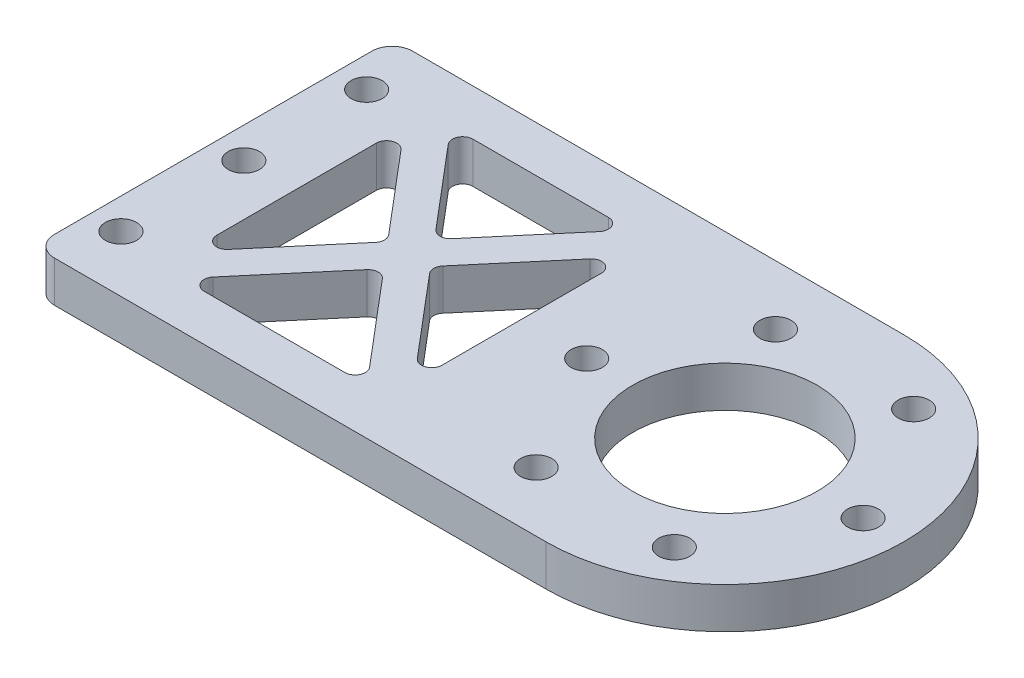
SolidWorks part; units mm, degrees
material "Thornel Mat VMA"
ref_plane "前视基准面" through (0, 0, 0) normal (0, 0, 1) x (1, 0, 0)
ref_plane "上视基准面" through (0, 0, 0) normal (0, 1, 0) x (1, 0, 0)
ref_plane "右视基准面" through (0, 0, 0) normal (1, 0, 0) x (0, 0, -1)
other "Configuration Table"
sketch "草图1" plane through (0, 0, 0) normal (0, 1, 0) x (1, 0, 0)
  line L1 (-25, -17.5) -> (25, -17.5)
  line L2 (-25, -17.5) -> (-25, 17.5)
  line L3 (-25, 17.5) -> (25, 17.5)
  line L4 (25, -17.5) -> (25, 17.5)
  line L5 (-25, -17.5) -> (25, 17.5) construction
  line L6 (-25, 17.5) -> (25, -17.5) construction
  circle A1 centre (25, 0) radius 17.5
  point P0 (0, 0)
  dimension "D1" = 35
  dimension "D2" = 35
  dimension "D3" = 50
extrude "凸台-拉伸1" add sketch "草图1" along normal blind 4 contours A1 L3 L2 L1 | L3 A1 L1 L4 | L1 A1 L3 L4
sketch "草图3" plane through (0, 4, 0) normal (0, 1, 0) x (1, 0, 0)
  circle A0 centre (25, 0) radius 13.5 construction
  circle A1 centre (38.5, 0) radius 1.525
  circle A2 centre (31.75, -11.6913) radius 1.525
  circle A3 centre (18.25, -11.6913) radius 1.525
  circle A4 centre (11.5, 0) radius 1.525
  circle A5 centre (18.25, 11.6913) radius 1.525
  circle A6 centre (31.75, 11.6913) radius 1.525
  point P6 (25, 0)
  point P17 (25, 0)
  dimension "D1" = 27
  dimension "D2" = 3.05
  dimension "D3" = 6
extrude "切除-拉伸2" cut sketch "草图3" against normal through all
sketch "草图4" plane through (0, 4, 0) normal (0, 1, 0) x (1, 0, 0)
  circle A0 centre (25, 0) radius 9
  dimension "D1" = 18
extrude "切除-拉伸3" cut sketch "草图4" against normal through all
sketch "草图5" plane through (0, 4, 0) normal (0, 1, 0) x (1, 0, 0)
  line L0 (-25, -17.5) -> (25, -17.5) construction
  line L1 (-17, -13) -> (5, -13)
  line L2 (-17, -13) -> (-17, 13)
  line L3 (-17, 13) -> (5, 13)
  line L4 (5, -13) -> (5, 13)
  line L5 (-17, -13) -> (5, 13) construction
  line L6 (-17, 13) -> (5, -13) construction
  line L7 (-25, -17.5) -> (-25, 17.5) construction
  line L8 (-18.1451, 12.0311) -> (3.8549, -13.9689)
  line L9 (-15.8549, -13.9689) -> (6.1451, 12.0311)
  line L10 (-15.7022, 14.0981) -> (6.2978, -11.9019)
  line L11 (-18.2978, -11.9019) -> (3.7022, 14.0981)
  point P0 (-6, 0)
  dimension "D1" = 4.5
  dimension "D2" = 8
  dimension "D3" = 22
  dimension "D4" = 1.5
  dimension "D5" = 1.7
extrude "切除-拉伸4" cut sketch "草图5" against normal through all contours L10 L11 L3 | L9 L10 L4 | L9 L1 L8 | L2 L11 L8
fillet "圆角1" radius 1 12 edges at (3.0351, 2, 13) (-15.0351, 2, 13) (2.7731, 2, -13) (-6, 2, -2.6318) (-14.7731, 2, -13) (5, 2, -10.6778) (5, 2, 10.3682) (-3.9041, 2, -0.1548) (-6, 2, 2.3222) (-8.0959, 2, -0.1548) (-17, 2, 10.3682) (-17, 2, -10.6778)
fillet "圆角2" radius 2 2 edges at (-25, 2, 17.5) (-25, 2, -17.5)
sketch "草图7" plane through (0, 4, 0) normal (0, 1, 0) x (1, 0, 0)
  line L0 (-22, 7.9868) -> (-22, 50007.9868) construction
  line L1 (-25, -15.5) -> (-25, 15.5) construction
  line L2 (0, 0) -> (50000, 0) construction
  circle A0 centre (-22, 0) radius 1.525
  circle A1 centre (-22, 12) radius 1.525
  circle A2 centre (-22, -12) radius 1.525
  dimension "D2" = 3.05
  dimension "D1" = 3
  dimension "D3" = 12
extrude "切除-拉伸5" cut sketch "草图7" against normal through all
